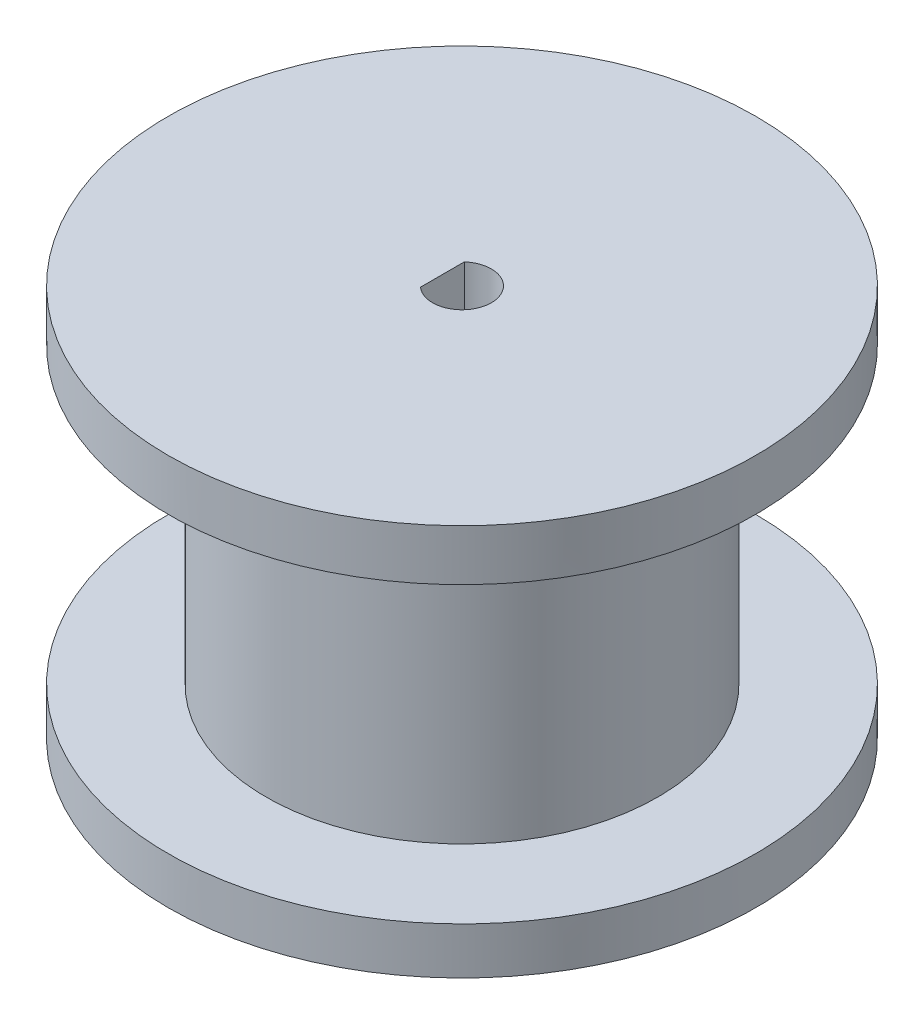
SolidWorks part; units mm, degrees
material "1060 合金"
ref_plane "前视基准面" through (0, 0, 0) normal (0, 0, 1) x (1, 0, 0)
ref_plane "上视基准面" through (0, 0, 0) normal (0, 1, 0) x (1, 0, 0)
ref_plane "右视基准面" through (0, 0, 0) normal (1, 0, 0) x (0, 0, -1)
sketch "草图1" plane through (0, 0, 0) normal (0, 1, 0) x (1, 0, 0)
  line L1 (-1, 0) -> (-1, 1.118)
  line L2 (-1, 0) -> (-1, -1.118)
  circle A0 centre (0, 0) radius 1.5
  circle A1 centre (0, 0) radius 15
extrude "凸台-拉伸1" add sketch "草图1" along normal blind 20 contours L1 A0 L2 | A1 A0 L1
sketch "草图2" plane through (0, 0, 0) normal (0, 0, 1) x (1, 0, 0)
  line L0 (0, 0) -> (0, 20)
  line L2 (15, 17.392) -> (10, 17.392)
  line L3 (15, 17.392) -> (15, 2.392)
  line L5 (10, 17.392) -> (10, 2.392)
  line L6 (10, 2.392) -> (15, 2.392)
revolve "切除-旋转1" cut sketch "草图2" angle 360 about L0
